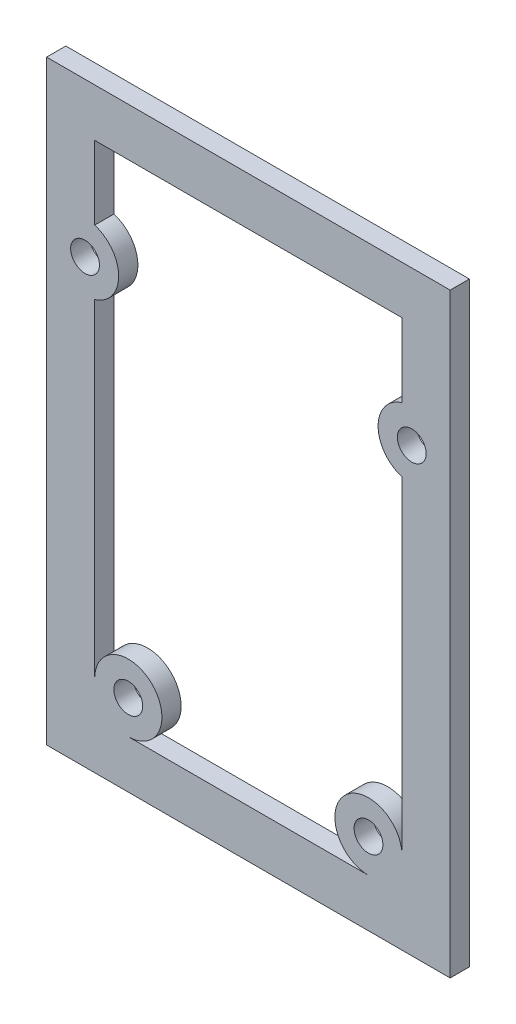
SolidWorks part; units mm, degrees
ref_plane "Front Plane" through (0, 0, 0) normal (0, 0, 1) x (1, 0, 0)
ref_plane "Top Plane" through (0, 0, 0) normal (0, 1, 0) x (1, 0, 0)
ref_plane "Right Plane" through (0, 0, 0) normal (1, 0, 0) x (0, 0, -1)
sketch "Sketch1" plane through (0, 0, 0) normal (0, 0, 1) x (1, 0, 0)
  line L11 (-81.6015, -26) -> (-39.6015, -26)
  line L12 (-81.6015, -26) -> (-81.6015, -88)
  line L13 (-81.6015, -88) -> (-39.6015, -88)
  line L14 (-39.6015, -26) -> (-39.6015, -88)
  line L39 (-76.6015, -31) -> (-76.6015, -38.6459)
  line L40 (-76.6015, -83) -> (-44.6015, -83)
  line L41 (-44.6015, -31) -> (-44.6015, -38.6459)
  line L42 (-76.6015, -31) -> (-44.6015, -31)
  line L75 (-60.6015, -26) -> (-60.6015, -88) construction
  line L76 (-44.6015, -45.3541) -> (-44.6015, -83)
  line L77 (-76.6015, -45.3541) -> (-76.6015, -83)
  line L78 (-44.6015, -31) -> (-44.6015, -83) construction
  line L80 (-76.6015, -31) -> (-76.6015, -83) construction
  circle A0 centre (-60.6015, -67) radius 23
  circle A4 centre (-77.6015, -42) radius 1.5
  circle A6 centre (-73.1015, -79.5) radius 1.5
  circle A7 centre (-43.6015, -42) radius 1.5
  circle A8 centre (-48.1015, -79.5) radius 1.5
  arc A17 (-76.6015, -45.3541) -> (-76.6015, -38.6459) centre (-77.6015, -42) ccw
  arc A18 (-44.6015, -45.3541) -> (-44.6015, -38.6459) centre (-43.6015, -42) cw
  circle A19 centre (-73.1015, -79.5) radius 3.5
  circle A20 centre (-48.1015, -79.5) radius 3.5
  circle A22 centre (-77.6015, -42) radius 3.5 construction
  circle A23 centre (-43.6015, -42) radius 3.5 construction
  point P61 (-74.5, -41)
  point P71 (-38.5, -41)
  dimension "D26" = 46
  dimension "D29" = 2
  dimension "D27" = 21
  dimension "D19" = 3
  dimension "D32" = 3
  dimension "D33" = 8.5
  dimension "D34" = 8.5
  dimension "D5" = 62
  dimension "D6" = 42
  dimension "D28" = 21
  dimension "D22" = 16
  dimension "D23" = 4
  dimension "D21" = 5
extrude "Boss-Extrude1" add sketch "Sketch1" along normal blind 2 contours A19 L77 L40 | A19 A6 | L76 A20 L40 | A20 A8 | L14 A0 L76 L40 L77 L12 L13 | A0 L12 L13 | A0 L13 L14 | A18 L76 A0 L14 L11 L12 L77 A17 L39 L42 L41 A4 A7
